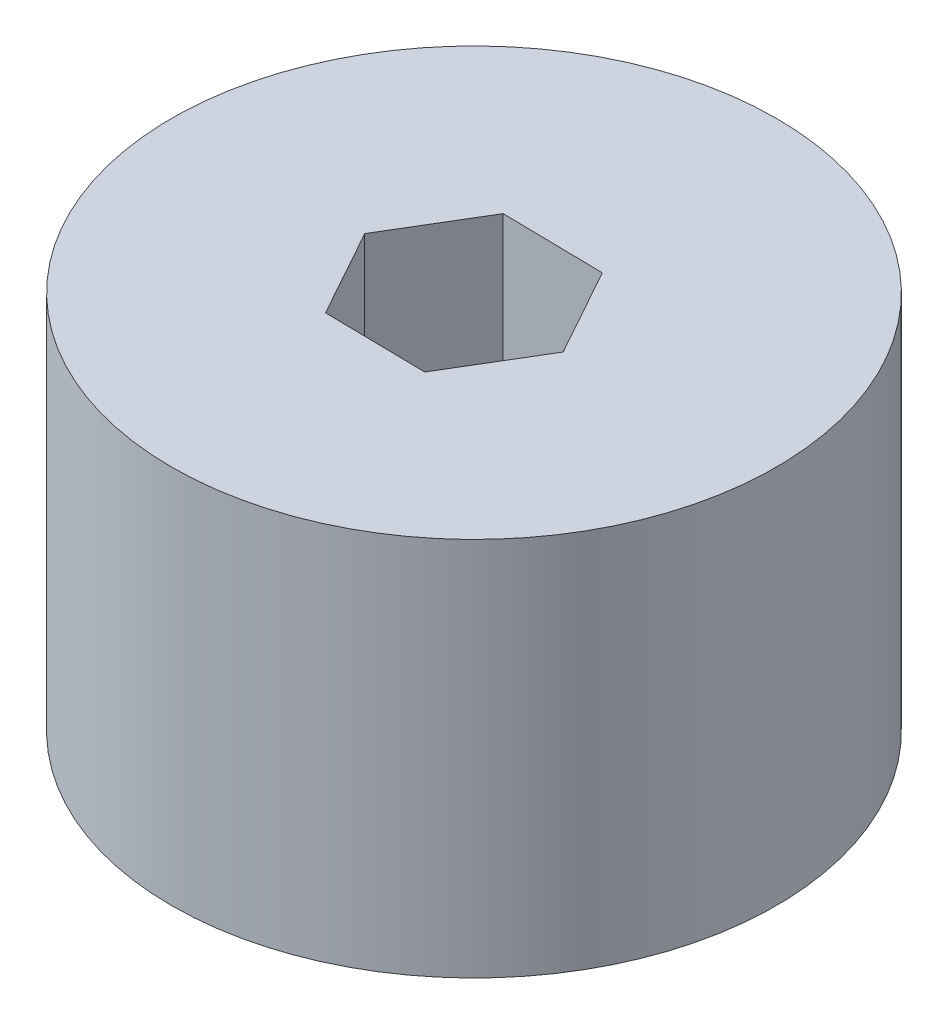
SolidWorks part; units mm, degrees
ref_plane "Front Plane" through (0, 0, 0) normal (0, 0, 1) x (1, 0, 0)
ref_plane "Top Plane" through (0, 0, 0) normal (0, 1, 0) x (1, 0, 0)
ref_plane "Right Plane" through (0, 0, 0) normal (1, 0, 0) x (0, 0, -1)
sketch "Sketch1" plane through (0, 0, 0) normal (0, 1, 0) x (1, 0, 0)
  line L0 (2.9455, -6.2396) -> (6.4146, -0.4537)
  line L1 (6.4146, -0.4537) -> (3.1383, 5.4436)
  line L2 (3.1383, 5.4436) -> (-3.607, 5.5549)
  line L3 (-3.607, 5.5549) -> (-7.0761, -0.2311)
  line L4 (-7.0761, -0.2311) -> (-3.7998, -6.1283)
  line L5 (-3.7998, -6.1283) -> (2.9455, -6.2396)
  circle A0 centre (0, 0) radius 20.21
  circle A1 centre (-0.3308, -0.3424) radius 5.8424 construction
extrude "Boss-Extrude1" add sketch "Sketch1" along normal blind 25.4
